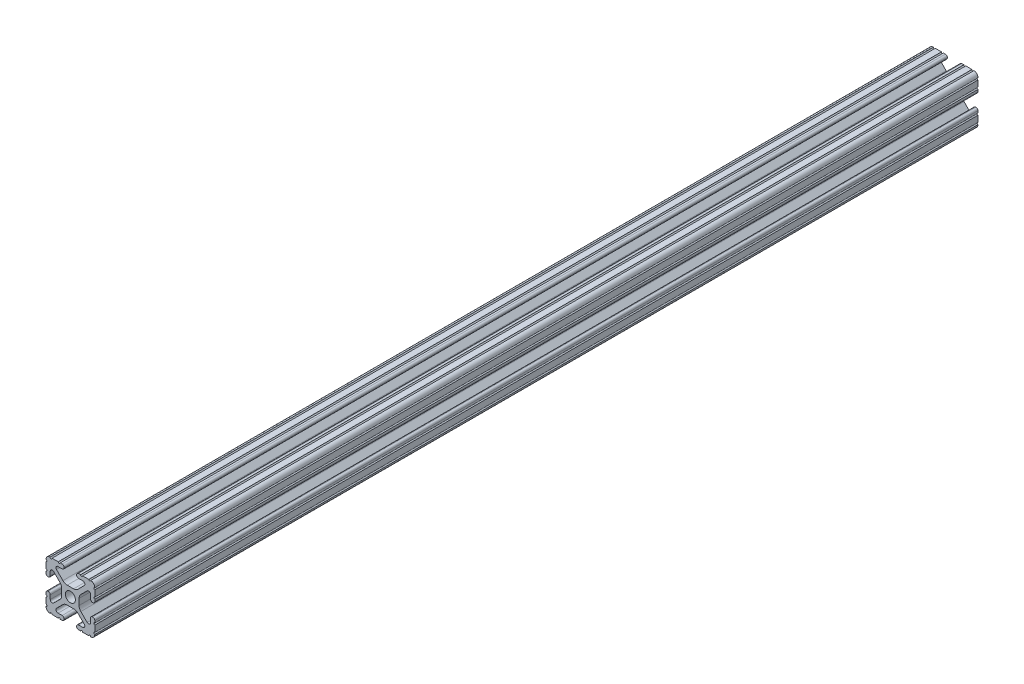
SolidWorks part; units mm, degrees
ref_plane "Front Plane" through (0, 0, 0) normal (0, 0, 1) x (1, 0, 0)
ref_plane "Top Plane" through (0, 0, 0) normal (0, 1, 0) x (1, 0, 0)
ref_plane "Right Plane" through (0, 0, 0) normal (1, 0, 0) x (0, 0, -1)
sketch "Sketch1" plane through (0, 0, 0) normal (0, 0, 1) x (1, 0, 0)
  line L88 (-7.1797, -8.6452) -> (-3.9523, -5.4237)
  line L89 (-1.7093, -4.4958) -> (1.7093, -4.4958)
  line L90 (3.9523, -5.4237) -> (7.1797, -8.6452)
  line L91 (6.4164, -10.4902) -> (4.2875, -10.4902)
  line L92 (3.2385, -11.5392) -> (3.2385, -11.651)
  line L93 (4.2875, -12.7) -> (5.3171, -12.7)
  line L94 (6.3331, -12.7) -> (9.5504, -12.7)
  line L95 (12.7, -9.5504) -> (12.7, -6.3331)
  line L96 (12.7, -5.3171) -> (12.7, -4.2875)
  line L97 (11.651, -3.2385) -> (11.5392, -3.2385)
  line L98 (10.4902, -4.2875) -> (10.4902, -6.4021)
  line L99 (8.7371, -7.1294) -> (5.441, -3.8408)
  line L100 (4.5085, -1.5932) -> (4.5085, 1.5932)
  line L101 (5.441, 3.8408) -> (8.7371, 7.1294)
  line L102 (10.4902, 6.4021) -> (10.4902, 4.2875)
  line L103 (11.5392, 3.2385) -> (11.651, 3.2385)
  line L104 (12.7, 4.2875) -> (12.7, 5.3171)
  line L105 (12.7, 6.3331) -> (12.7, 9.5504)
  line L106 (9.5504, 12.7) -> (6.3331, 12.7)
  line L107 (5.3171, 12.7) -> (4.2875, 12.7)
  line L108 (3.2385, 11.651) -> (3.2385, 11.5392)
  line L109 (4.2875, 10.4902) -> (6.4768, 10.4902)
  line L110 (7.207, 8.7244) -> (3.8983, 5.4232)
  line L111 (1.6558, 4.4958) -> (-1.6558, 4.4958)
  line L112 (-3.8983, 5.4232) -> (-7.207, 8.7244)
  line L113 (-6.4768, 10.4902) -> (-4.2875, 10.4902)
  line L114 (-3.2385, 11.5392) -> (-3.2385, 11.651)
  line L115 (-4.2875, 12.7) -> (-5.3171, 12.7)
  line L116 (-6.3331, 12.7) -> (-9.5504, 12.7)
  line L117 (-12.7, 9.5504) -> (-12.7, 6.3331)
  line L118 (-12.7, 5.3171) -> (-12.7, 4.2875)
  line L119 (-11.651, 3.2385) -> (-11.5392, 3.2385)
  line L120 (-10.4902, 4.2875) -> (-10.4902, 6.4021)
  line L121 (-8.7371, 7.1294) -> (-5.441, 3.8408)
  line L122 (-4.5085, 1.5932) -> (-4.5085, -1.5932)
  line L123 (-5.441, -3.8408) -> (-8.7371, -7.1294)
  line L124 (-10.4902, -6.4021) -> (-10.4902, -4.2875)
  line L125 (-11.5392, -3.2385) -> (-11.651, -3.2385)
  line L126 (-12.7, -4.2875) -> (-12.7, -5.3171)
  line L127 (-12.7, -6.3331) -> (-12.7, -9.5504)
  line L128 (-9.5504, -12.7) -> (-6.3331, -12.7)
  line L129 (-5.3171, -12.7) -> (-4.2875, -12.7)
  line L130 (-3.2385, -11.651) -> (-3.2385, -11.5392)
  line L131 (-4.2875, -10.4902) -> (-6.4164, -10.4902)
  circle A1 centre (0, 0) radius 2.6035
  arc A104 (-7.1797, -8.6452) -> (-6.4164, -10.4902) centre (-6.4164, -9.4098) ccw
  arc A105 (-1.7093, -4.4958) -> (-3.9523, -5.4237) centre (-1.7093, -7.6708) ccw
  arc A106 (3.9523, -5.4237) -> (1.7093, -4.4958) centre (1.7093, -7.6708) ccw
  arc A107 (6.4164, -10.4902) -> (7.1797, -8.6452) centre (6.4164, -9.4098) ccw
  arc A108 (4.2875, -10.4902) -> (3.2385, -11.5392) centre (4.2875, -11.5392) ccw
  arc A109 (3.2385, -11.651) -> (4.2875, -12.7) centre (4.2875, -11.651) ccw
  arc A110 (6.3331, -12.7) -> (5.3171, -12.7) centre (5.8251, -12.7) ccw
  arc A111 (10.5664, -12.6998) -> (9.5504, -12.7) centre (10.0584, -12.7) ccw
  arc A112 (10.5664, -12.6998) -> (12.6998, -10.5664) centre (10.5918, -10.5918) ccw
  arc A113 (12.7, -9.5504) -> (12.6998, -10.5664) centre (12.7, -10.0584) ccw
  arc A114 (12.7, -5.3171) -> (12.7, -6.3331) centre (12.7, -5.8251) ccw
  arc A115 (12.7, -4.2875) -> (11.651, -3.2385) centre (11.651, -4.2875) ccw
  arc A116 (11.5392, -3.2385) -> (10.4902, -4.2875) centre (11.5392, -4.2875) ccw
  arc A117 (8.7371, -7.1294) -> (10.4902, -6.4021) centre (9.4628, -6.4021) ccw
  arc A118 (4.5085, -1.5932) -> (5.441, -3.8408) centre (7.6835, -1.5932) ccw
  arc A119 (5.441, 3.8408) -> (4.5085, 1.5932) centre (7.6835, 1.5932) ccw
  arc A120 (10.4902, 6.4021) -> (8.7371, 7.1294) centre (9.4628, 6.4021) ccw
  arc A121 (10.4902, 4.2875) -> (11.5392, 3.2385) centre (11.5392, 4.2875) ccw
  arc A122 (11.651, 3.2385) -> (12.7, 4.2875) centre (11.651, 4.2875) ccw
  arc A123 (12.7, 6.3331) -> (12.7, 5.3171) centre (12.7, 5.8251) ccw
  arc A124 (12.6998, 10.5664) -> (12.7, 9.5504) centre (12.7, 10.0584) ccw
  arc A125 (12.6998, 10.5664) -> (10.5664, 12.6998) centre (10.5918, 10.5918) ccw
  arc A126 (9.5504, 12.7) -> (10.5664, 12.6998) centre (10.0584, 12.7) ccw
  arc A127 (5.3171, 12.7) -> (6.3331, 12.7) centre (5.8251, 12.7) ccw
  arc A128 (4.2875, 12.7) -> (3.2385, 11.651) centre (4.2875, 11.651) ccw
  arc A129 (3.2385, 11.5392) -> (4.2875, 10.4902) centre (4.2875, 11.5392) ccw
  arc A130 (7.207, 8.7244) -> (6.4768, 10.4902) centre (6.4768, 9.4563) ccw
  arc A131 (1.6558, 4.4958) -> (3.8983, 5.4232) centre (1.6558, 7.6708) ccw
  arc A132 (-3.8983, 5.4232) -> (-1.6558, 4.4958) centre (-1.6558, 7.6708) ccw
  arc A133 (-6.4768, 10.4902) -> (-7.207, 8.7244) centre (-6.4768, 9.4563) ccw
  arc A134 (-4.2875, 10.4902) -> (-3.2385, 11.5392) centre (-4.2875, 11.5392) ccw
  arc A135 (-3.2385, 11.651) -> (-4.2875, 12.7) centre (-4.2875, 11.651) ccw
  arc A136 (-6.3331, 12.7) -> (-5.3171, 12.7) centre (-5.8251, 12.7) ccw
  arc A137 (-10.5664, 12.6998) -> (-9.5504, 12.7) centre (-10.0584, 12.7) ccw
  arc A138 (-10.5664, 12.6998) -> (-12.6998, 10.5664) centre (-10.5918, 10.5918) ccw
  arc A139 (-12.7, 9.5504) -> (-12.6998, 10.5664) centre (-12.7, 10.0584) ccw
  arc A140 (-12.7, 5.3171) -> (-12.7, 6.3331) centre (-12.7, 5.8251) ccw
  arc A141 (-12.7, 4.2875) -> (-11.651, 3.2385) centre (-11.651, 4.2875) ccw
  arc A142 (-11.5392, 3.2385) -> (-10.4902, 4.2875) centre (-11.5392, 4.2875) ccw
  arc A143 (-8.7371, 7.1294) -> (-10.4902, 6.4021) centre (-9.4628, 6.4021) ccw
  arc A144 (-4.5085, 1.5932) -> (-5.441, 3.8408) centre (-7.6835, 1.5932) ccw
  arc A145 (-5.441, -3.8408) -> (-4.5085, -1.5932) centre (-7.6835, -1.5932) ccw
  arc A146 (-10.4902, -6.4021) -> (-8.7371, -7.1294) centre (-9.4628, -6.4021) ccw
  arc A147 (-10.4902, -4.2875) -> (-11.5392, -3.2385) centre (-11.5392, -4.2875) ccw
  arc A148 (-11.651, -3.2385) -> (-12.7, -4.2875) centre (-11.651, -4.2875) ccw
  arc A149 (-12.7, -6.3331) -> (-12.7, -5.3171) centre (-12.7, -5.8251) ccw
  arc A150 (-12.6998, -10.5664) -> (-12.7, -9.5504) centre (-12.7, -10.0584) ccw
  arc A151 (-12.6998, -10.5664) -> (-10.5664, -12.6998) centre (-10.5918, -10.5918) ccw
  arc A152 (-9.5504, -12.7) -> (-10.5664, -12.6998) centre (-10.0584, -12.7) ccw
  arc A153 (-5.3171, -12.7) -> (-6.3331, -12.7) centre (-5.8251, -12.7) ccw
  arc A154 (-4.2875, -12.7) -> (-3.2385, -11.651) centre (-4.2875, -11.651) ccw
  arc A155 (-3.2385, -11.5392) -> (-4.2875, -10.4902) centre (-4.2875, -11.5392) ccw
extrude "Boss-Extrude1" add sketch "Sketch1" along normal mid plane 459.74
